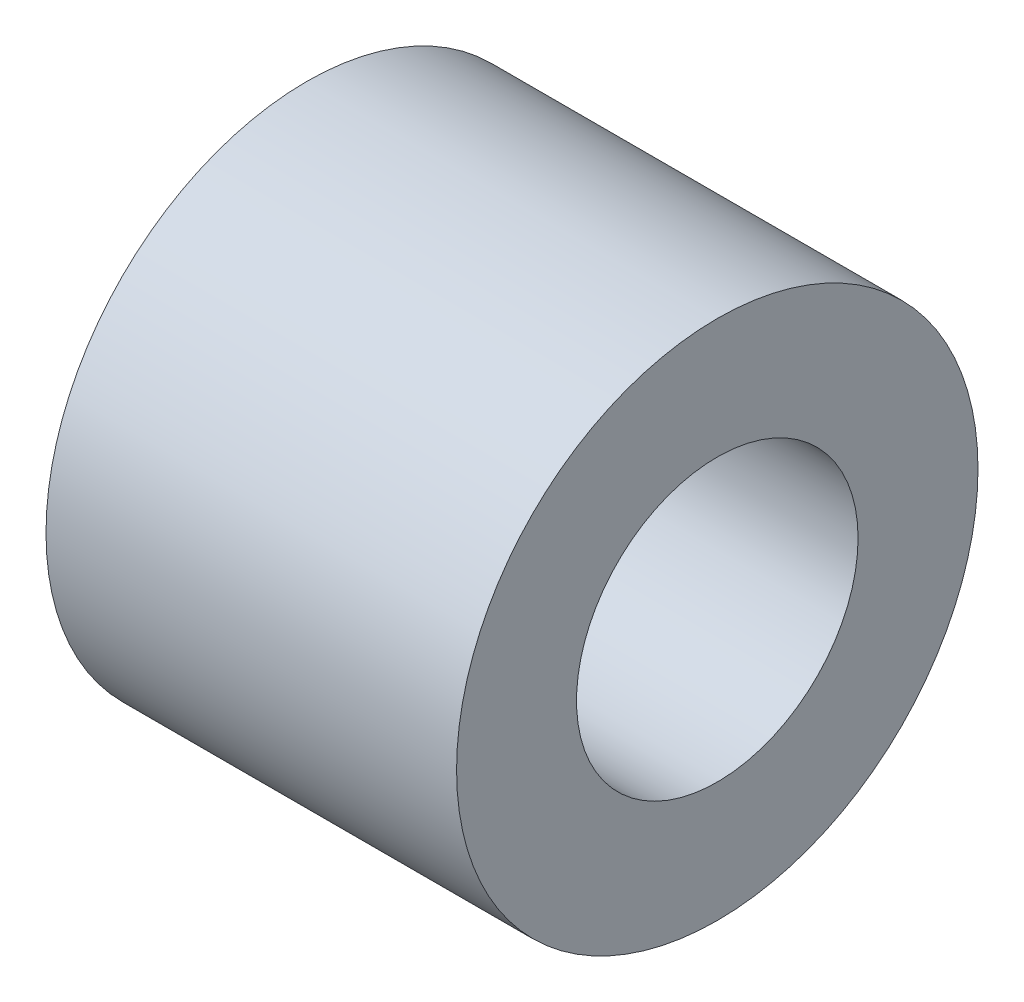
SolidWorks part; units mm, degrees
ref_plane "Plan de face" through (0, 0, 0) normal (0, 0, 1) x (1, 0, 0)
ref_plane "Plan de dessus" through (0, 0, 0) normal (0, 1, 0) x (1, 0, 0)
ref_plane "Plan de droite" through (0, 0, 0) normal (1, 0, 0) x (0, 0, -1)
sketch "Esquisse1" plane through (0, 0, 0) normal (1, 0, 0) x (0, 0, -1)
  circle A0 centre (0, 0) radius 3.429
  circle A1 centre (0, 0) radius 6.35
  dimension "D1" = 6.858
  dimension "D2" = 12.7
extrude "Boss.-Extru.1" add sketch "Esquisse1" against normal blind 10
equation "\"D1@Boss.-Extru.1\"=10mm"
